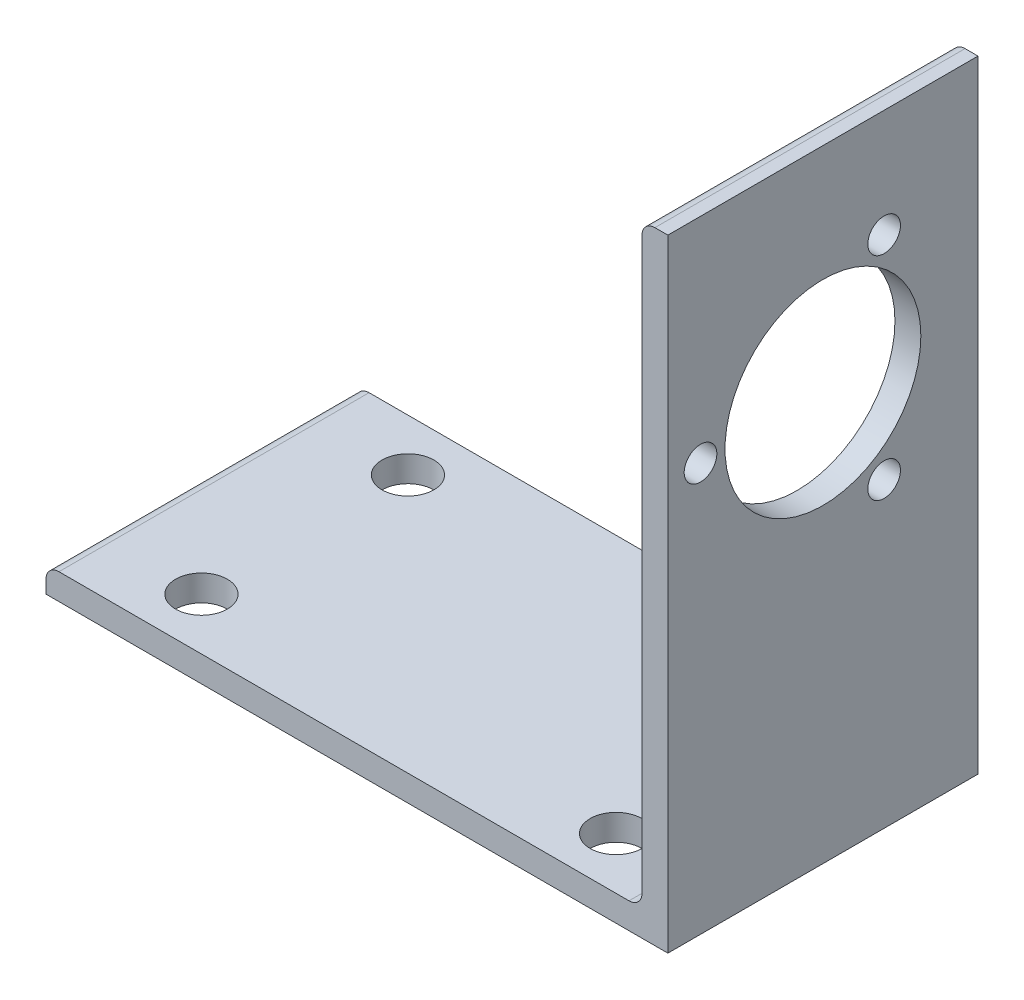
SolidWorks part; units mm, degrees
material "McMaster 6061-T6"
ref_plane "Front Plane" through (0, 0, 0) normal (0, 0, 1) x (1, 0, 0)
ref_plane "Top Plane" through (0, 0, 0) normal (0, 1, 0) x (1, 0, 0)
ref_plane "Right Plane" through (0, 0, 0) normal (1, 0, 0) x (0, 0, -1)
sketch "Sketch2" plane through (0, 0, 0) normal (0, 0, 1) x (1, 0, 0)
  line L0 (-19.05, 0) -> (19.05, 0)
  line L1 (19.05, 0) -> (19.05, 38.1)
  line L2 (19.05, 38.1) -> (17.4625, 38.1) construction
  line L3 (17.4625, 37.3062) -> (17.4625, 2.3812)
  line L4 (16.6688, 1.5875) -> (-18.2563, 1.5875)
  line L5 (-19.05, 0) -> (-19.05, 1.5875) construction
  line L6 (18.2563, 38.1) -> (19.05, 38.1)
  line L7 (-19.05, 0.7937) -> (-19.05, 0)
  arc A0 (17.4625, 37.3062) -> (18.2563, 38.1) centre (18.2563, 37.3062) cw
  arc A1 (-19.05, 0.7937) -> (-18.2563, 1.5875) centre (-18.2563, 0.7937) cw
  arc A2 (17.4625, 2.3812) -> (16.6688, 1.5875) centre (16.6688, 2.3812) cw
  dimension "Vert" = 38.1
  dimension "Horz" = 38.1
  dimension "Thickness" = 1.5875
ref_plane "Plane1" through (19.05, 0, 0) normal (1, 0, 0) x (0, 0, -1)
sketch "Sketch3" plane through (19.05, 0, 0) normal (1, 0, 0) x (0, 0, -1)
  line L0 (0, 0) -> (0, 38.1) construction
  circle A0 centre (9.5, 25) radius 5.9995
  line B0 (39.5, 0) -> (-20.5, 0)
  arc B1 (0, 25) -> (19, 25) centre (9.5, 25) ccw
  arc B2 (0, 25) -> (19, 25) centre (9.5, 25) ccw
  arc B3 (19, 25) -> (0, 25) centre (9.5, 25) ccw
  arc B4 (19, 25) -> (0, 25) centre (9.5, 25) ccw
  line B5 (9.5, 25) -> (9.5, -9.8692) construction
  arc B6 (13.75, 32.3612) -> (12.75, 30.6292) centre (13.25, 31.4952) cw
  arc B7 (12.75, 30.6292) -> (13.75, 32.3612) centre (13.25, 31.4952) cw
  arc B8 (3, 25) -> (1, 25) centre (2, 25) cw
  arc B9 (1, 25) -> (3, 25) centre (2, 25) cw
  arc B10 (13.75, 17.6388) -> (12.75, 19.3708) centre (13.25, 18.5048) cw
  arc B11 (12.75, 19.3708) -> (13.75, 17.6388) centre (13.25, 18.5048) cw
  dimension "D1" = 11.999
sketch_block_instance "Block-L-Bracket Motor Mounting 1.5in-1"
sketch_block "Block-L-Bracket Motor Mounting 1.5in"
extrude "Boss-Extrude1" add sketch "Sketch2" against normal up to vertex (19 mm away)
extrude "Cut-Extrude1" cut sketch "Sketch3" against normal up to next contours A0 | B7 B6 | B11 B10 | B9 B8
sketch "Top View" plane through (0, 0, 0) normal (0, -1, 0) x (1, 0, 0)
  line L1 (-12.7, -15.825) -> (12.7, -15.825) construction
  line L2 (-12.7, -15.825) -> (-12.7, -3.175) construction
  line L3 (-12.7, -3.175) -> (12.7, -3.175) construction
  line L4 (19.05, 0) -> (-19.05, 0)
  line L5 (-19.05, 0) -> (-19.05, -19)
  line L6 (-19.05, -19) -> (19.05, -19)
  line L7 (19.05, -19) -> (19.05, 0)
  line L8 (19.05, 0) -> (-19.05, 0) construction
  line L9 (-19.05, 0) -> (-19.05, -19) construction
  line L10 (-19.05, -19) -> (19.05, -19) construction
  line L11 (19.05, -19) -> (19.05, 0) construction
  line L12 (12.7, -15.825) -> (12.7, -3.175) construction
  circle A0 centre (-12.7, -15.825) radius 1.5875
  circle A1 centre (12.7, -15.825) radius 1.5875
  circle A2 centre (12.7, -3.175) radius 1.5875
  circle A3 centre (-12.7, -3.175) radius 1.5875
  point P12 (0, -15.825)
  point P13 (0, -19)
  point P14 (-12.7, -9.5)
  point P15 (-19.05, -9.5)
  dimension "D4" = 3.175
  dimension "D2" = 38.1
  dimension "D3" = 19
  dimension "D5" = 6.35
  dimension "D6" = 3.175
  dimension "D1" = 0
extrude "Cut-Extrude2" cut sketch "Top View" against normal up to next contours L2 A0 L1 | L1 A1 L12 | L12 A2 L3 | L3 A3 L2
